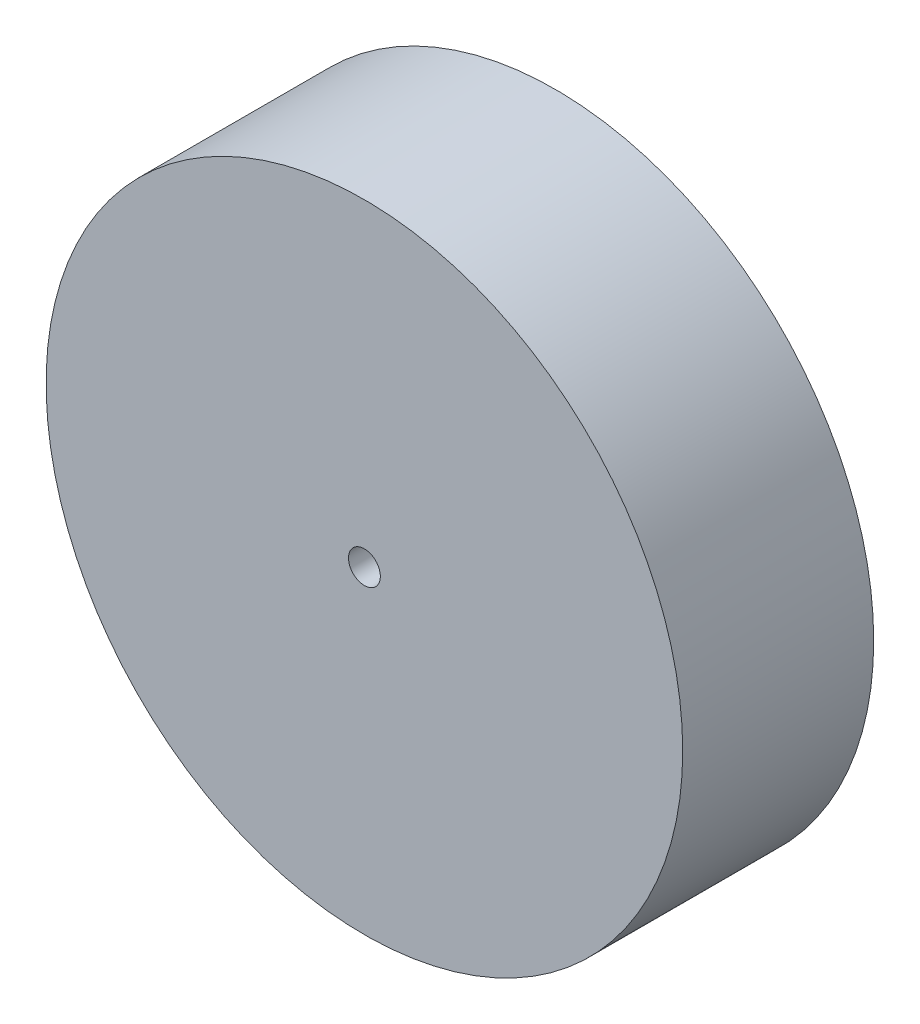
SolidWorks part; units mm, degrees
material "ABS"
ref_plane "Front Plane" through (0, 0, 0) normal (0, 0, 1) x (1, 0, 0)
ref_plane "Top Plane" through (0, 0, 0) normal (0, 1, 0) x (1, 0, 0)
ref_plane "Right Plane" through (0, 0, 0) normal (1, 0, 0) x (0, 0, -1)
sketch "Sketch1" plane through (0, 0, 0) normal (0, 0, 1) x (1, 0, 0)
  circle A0 centre (0, 0) radius 50
  dimension "D1" = 100
extrude "Boss-Extrude1" add sketch "Sketch1" along normal blind 30
sketch "Sketch2" plane through (0, 0, 0) normal (0, 0, -1) x (-1, 0, 0)
  circle A0 centre (0, 0) radius 2.5
  dimension "D1" = 5
extrude "Cut-Extrude1" cut sketch "Sketch2" against normal through all
shell "Shell1" thickness 10
